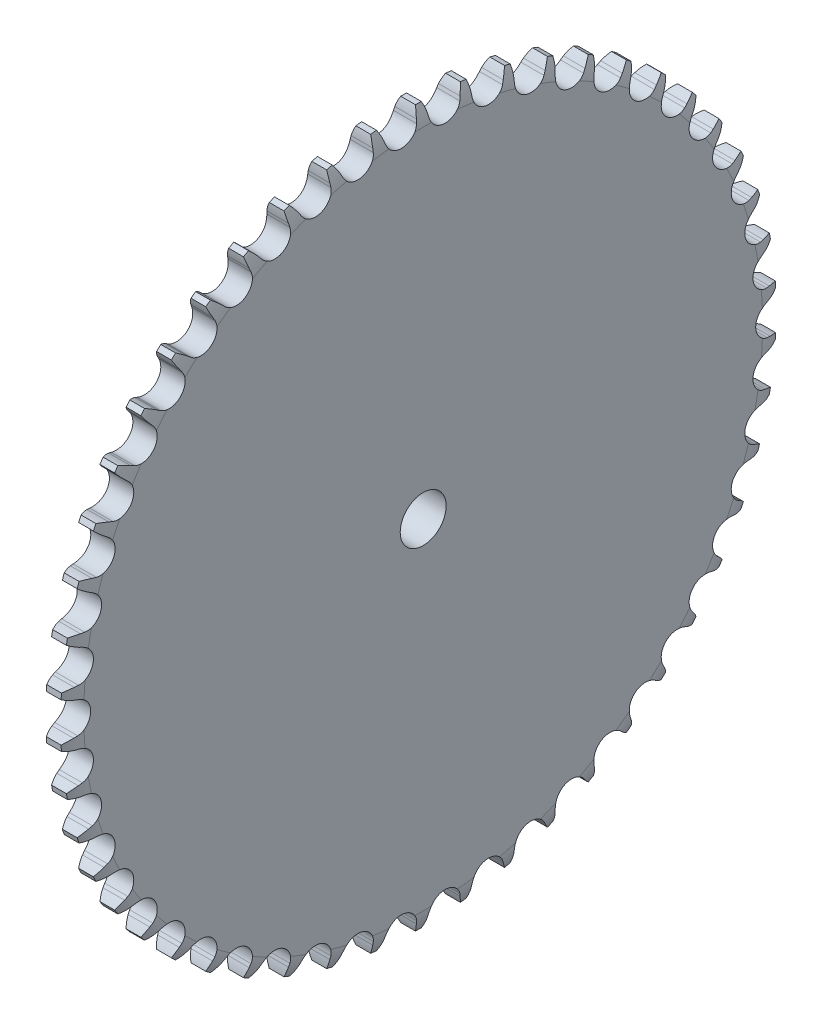
SolidWorks part; units mm, degrees
ref_plane "Front Plane" through (0, 0, 0) normal (0, 0, 1) x (1, 0, 0)
ref_plane "Top Plane" through (0, 0, 0) normal (0, 1, 0) x (1, 0, 0)
ref_plane "Right Plane" through (0, 0, 0) normal (1, 0, 0) x (0, 0, -1)
sketch "Sketch1" plane through (0, 0, 0) normal (0, 0, 1) x (1, 0, 0)
  line L0 (0, 0) -> (0, 73.8414)
  line L1 (-1.0423, 77.85) -> (-4.2577, 77.85)
  line L2 (-5.3, 73.8414) -> (-5.3, 20)
  line L3 (-5.3, 20) -> (-35.3, 20)
  line L4 (-35.3, 20) -> (-35.3, 0)
  line L5 (-35.3, 0) -> (0, 0)
  line L6 (0, 0) -> (22.8181, 0) construction
  arc A0 (-5.3, 73.8414) -> (-4.2577, 77.85) centre (4.6895, 73.3839) cw
  arc A1 (0, 73.8414) -> (-1.0423, 77.85) centre (-9.9895, 73.3839) ccw
  dimension "D5" = 10
  dimension "D1" = 35.3
  dimension "D2" = 30
  dimension "D3" = 20
  dimension "D4" = 155.7
revolve "Revolve1" add sketch "Sketch1" angle 360 about L6
sketch "Sketch2" plane through (-35.3, 0, 0) normal (-1, 0, 0) x (0, 0, 1)
  circle A0 centre (0, 0) radius 5
  dimension "D1" = 10
extrude "Cut-Extrude1" cut sketch "Sketch2" against normal blind 93
sketch "Sketch4" plane through (-35.3, 0, 0) normal (-1, 0, 0) x (0, 0, 1)
  line L0 (0, 0) -> (0, 75.845) construction
  line L1 (0, 0) -> (-4.7625, 75.6953) construction
  line L2 (0, 0) -> (4.7625, 75.6953) construction
  line L3 (-1.1837, 75.8358) -> (-1.3157, 75.0876)
  line L4 (1.1837, 75.8358) -> (1.3157, 75.0876)
  line L5 (-8.3306, 75.3861) -> (-8.106, 74.6603)
  arc A0 (-8.3306, 75.3861) -> (-1.1837, 75.8358) centre (0, 0) ccw
  arc A1 (-8.106, 74.6603) -> (-1.3157, 75.0876) centre (-4.7625, 75.6953) ccw
  circle A2 centre (4.7625, 75.6953) radius 3.5
  arc A3 (-1.1837, 75.8358) -> (-0.628, 77.8475) centre (9.6491, 73.9256) cw
  circle A4 centre (0, 0) radius 77.85 construction
  arc A5 (1.1837, 75.8358) -> (0.628, 77.8475) centre (-9.6491, 73.9256) ccw
  arc A6 (-8.3306, 75.3861) -> (-9.1342, 77.3123) centre (-18.8387, 72.1333) ccw
  arc A7 (-9.1342, 77.3123) -> (-0.628, 77.8475) centre (0, 0) cw
  dimension "D1" = 151.69
  dimension "D3" = 7
  dimension "D4" = 7
  dimension "D6" = 11
  dimension "D2" = 9.525
  dimension "D5" = 20
extrude "Cut-Extrude2" cut sketch "Sketch4" against normal blind 50 contours A7 A3 L3 A1 L5 A6
pattern_circular "CirPattern2" count 50 over 360 about axis through (0, 0, 0) along (1, 0, 0) of "Cut-Extrude2"
sketch "Sketch5" plane through (-35.3, 0, 0) normal (-1, 0, 0) x (0, 0, 1)
  circle A0 centre (0, 0) radius 20
extrude "Cut-Extrude3" cut sketch "Sketch5" against normal blind 30
sketch "Sketch6" plane through (-5.3, 0, 0) normal (-1, 0, 0) x (0, 0, 1)
  circle A0 centre (0, 0) radius 20
  dimension "D1" = 40
extrude "Boss-Extrude1" add sketch "Sketch6" along normal blind 10
sketch "Sketch8" plane through (-15.3, 0, 0) normal (-1, 0, 0) x (0, 0, 1)
  circle A0 centre (0, 0) radius 16.562
  circle A1 centre (0, 0) radius 15.922
  dimension "D1" = 33.124
  dimension "D2" = 31.844
sketch "Sketch11" plane through (-15.3, 0, 0) normal (-1, 0, 0) x (0, 0, 1)
  line L0 (0, 0) -> (0, 15.922) construction
  line L1 (0, 15.922) -> (0, 16.562) construction
  line L2 (0, 0) -> (0.9761, 15.8921) construction
  line L3 (0.9761, 15.8921) -> (1.0154, 16.5308) construction
  line L4 (-0.6409, 15.9091) -> (-0.4495, 16.5559)
  line L5 (0.6409, 15.9091) -> (0.4495, 16.5559)
  line L6 (1.3109, 15.8679) -> (1.58, 16.4865) construction
  line L7 (1.319, 15.8673) -> (1.5884, 16.4857)
  line L8 (2.5911, 15.7098) -> (2.4806, 16.3752)
  line L9 (3.2589, 15.5849) -> (3.6023, 16.1655)
  line L10 (4.502, 15.2723) -> (4.4741, 15.9462)
  line L11 (5.1494, 15.0663) -> (5.5615, 15.6003)
  line L12 (6.3447, 14.6033) -> (6.3998, 15.2755)
  line L13 (6.9618, 14.3193) -> (7.4365, 14.7986)
  line L14 (8.0911, 13.7129) -> (8.2285, 14.3733)
  line L15 (8.6688, 13.3553) -> (9.1987, 13.7726)
  line L16 (9.715, 12.6147) -> (9.9324, 13.2532)
  line L17 (10.2443, 12.1887) -> (10.8215, 12.5378)
  line L18 (11.1915, 11.3252) -> (11.4858, 11.9321)
  line L19 (11.6645, 10.8375) -> (12.2802, 11.1129)
  line L20 (12.4984, 9.864) -> (12.8651, 10.4302)
  line L21 (12.9078, 9.3219) -> (13.5527, 9.5196)
  line L22 (13.6159, 8.2534) -> (14.0493, 8.7702)
  line L23 (13.9556, 7.665) -> (14.6199, 7.782)
  line L24 (14.5269, 6.5176) -> (15.0206, 6.9772)
  line L25 (14.7917, 5.8919) -> (15.4654, 5.9264)
  line L26 (15.2177, 4.683) -> (15.7642, 5.0785)
  line L27 (15.4037, 4.0296) -> (16.0764, 3.9809)
  line L28 (15.6779, 2.7774) -> (16.2688, 3.1028)
  line L29 (15.7821, 2.1061) -> (16.4438, 1.9752)
  line L30 (15.9004, 0.8297) -> (16.5267, 1.08)
  line L31 (15.9213, 0.1507) -> (16.5619, -0.0606)
  line L32 (15.8818, -1.1305) -> (16.5342, -0.9591)
  line L33 (15.8191, -1.807) -> (16.4289, -2.0954)
  line L34 (15.6225, -3.0736) -> (16.291, -2.9837)
  line L35 (15.4772, -3.7373) -> (16.0469, -4.0984)
  line L36 (15.1264, -4.9702) -> (15.8009, -4.9631)
  line L37 (14.9006, -5.6109) -> (15.4216, -6.0393)
  line L38 (14.401, -6.7914) -> (15.0712, -6.8672)
  line L39 (14.0981, -7.3995) -> (14.5626, -7.8887)
  line L40 (13.4572, -8.5096) -> (14.1131, -8.6672)
  line L41 (13.082, -9.0759) -> (13.4828, -9.6184)
  line L42 (12.3095, -10.0988) -> (12.941, -10.3359)
  line L43 (11.8675, -10.6147) -> (12.1986, -11.2024)
  line L44 (10.9752, -11.535) -> (11.5728, -11.8478)
  line L45 (10.4731, -11.9927) -> (10.7295, -12.6166)
  line L46 (9.4745, -12.7963) -> (10.0291, -13.1802)
  line L47 (8.92, -13.1888) -> (9.0977, -13.8395)
  line L48 (7.8301, -13.8636) -> (8.3334, -14.3127)
  line L49 (7.2316, -14.185) -> (7.3281, -14.8526)
  line L50 (6.0671, -14.7207) -> (6.5114, -15.2283)
  line L51 (5.4336, -14.9662) -> (5.4473, -15.6405)
  line L52 (4.2121, -15.3547) -> (4.5906, -15.9131)
  line L53 (3.5533, -15.5204) -> (3.484, -16.1914)
  line L54 (2.2933, -15.756) -> (2.6003, -16.3566)
  line L55 (1.6191, -15.8395) -> (1.4678, -16.4968)
  line L56 (0.3397, -15.9184) -> (0.5705, -16.5522)
  line L57 (-0.3397, -15.9184) -> (-0.5705, -16.5522)
  line L58 (-1.6191, -15.8395) -> (-1.4678, -16.4968)
  line L59 (-2.2933, -15.756) -> (-2.6003, -16.3566)
  line L60 (-3.5533, -15.5204) -> (-3.484, -16.1914)
  line L61 (-4.2121, -15.3547) -> (-4.5906, -15.9131)
  line L62 (-5.4336, -14.9662) -> (-5.4473, -15.6405)
  line L63 (-6.0671, -14.7207) -> (-6.5114, -15.2283)
  line L64 (-7.2316, -14.185) -> (-7.3281, -14.8526)
  line L65 (-7.8301, -13.8636) -> (-8.3334, -14.3127)
  line L66 (-8.92, -13.1888) -> (-9.0977, -13.8395)
  line L67 (-9.4745, -12.7963) -> (-10.0291, -13.1802)
  line L68 (-10.4731, -11.9927) -> (-10.7295, -12.6166)
  line L69 (-10.9752, -11.535) -> (-11.5728, -11.8478)
  line L70 (-11.8675, -10.6147) -> (-12.1986, -11.2024)
  line L71 (-12.3095, -10.0988) -> (-12.941, -10.3359)
  line L72 (-13.082, -9.0759) -> (-13.4828, -9.6184)
  line L73 (-13.4572, -8.5096) -> (-14.1131, -8.6672)
  line L74 (-14.0981, -7.3995) -> (-14.5626, -7.8887)
  line L75 (-14.401, -6.7914) -> (-15.0712, -6.8672)
  line L76 (-14.9006, -5.6109) -> (-15.4216, -6.0393)
  line L77 (-15.1264, -4.9702) -> (-15.8009, -4.9631)
  line L78 (-15.4772, -3.7373) -> (-16.0469, -4.0984)
  line L79 (-15.6225, -3.0736) -> (-16.291, -2.9837)
  line L80 (-15.8191, -1.807) -> (-16.4289, -2.0954)
  line L81 (-15.8818, -1.1305) -> (-16.5342, -0.9591)
  line L82 (-15.9213, 0.1507) -> (-16.5619, -0.0606)
  line L83 (-15.9004, 0.8297) -> (-16.5267, 1.08)
  line L84 (-15.7821, 2.1061) -> (-16.4438, 1.9752)
  line L85 (-15.6779, 2.7774) -> (-16.2688, 3.1028)
  line L86 (-15.4037, 4.0296) -> (-16.0764, 3.9809)
  line L87 (-15.2177, 4.683) -> (-15.7642, 5.0785)
  line L88 (-14.7917, 5.8919) -> (-15.4654, 5.9264)
  line L89 (-14.5269, 6.5176) -> (-15.0206, 6.9772)
  line L90 (-13.9556, 7.665) -> (-14.6199, 7.782)
  line L91 (-13.6159, 8.2534) -> (-14.0493, 8.7702)
  line L92 (-12.9078, 9.3219) -> (-13.5527, 9.5196)
  line L93 (-12.4984, 9.864) -> (-12.8651, 10.4302)
  line L94 (-11.6645, 10.8375) -> (-12.2802, 11.1129)
  line L95 (-11.1915, 11.3252) -> (-11.4858, 11.9321)
  line L96 (-10.2443, 12.1887) -> (-10.8215, 12.5378)
  line L97 (-9.715, 12.6147) -> (-9.9324, 13.2532)
  line L98 (-8.6688, 13.3553) -> (-9.1987, 13.7726)
  line L99 (-8.0911, 13.7129) -> (-8.2285, 14.3733)
  line L100 (-6.9618, 14.3193) -> (-7.4365, 14.7986)
  line L101 (-6.3447, 14.6033) -> (-6.3998, 15.2755)
  line L102 (-5.1494, 15.0663) -> (-5.5615, 15.6003)
  line L103 (-4.502, 15.2723) -> (-4.4741, 15.9462)
  line L104 (-3.2589, 15.5849) -> (-3.6023, 16.1655)
  line L105 (-2.5911, 15.7098) -> (-2.4806, 16.3752)
  line L106 (-1.319, 15.8673) -> (-1.5884, 16.4857)
  circle A0 centre (0, 0) radius 15.922 construction
  circle A1 centre (0, 0) radius 16.562 construction
  arc A2 (0.4495, 16.5559) -> (0, 16.562) centre (0, 0) ccw
  arc A4 (-0.6409, 15.9091) -> (-1.319, 15.8673) centre (0, 0) ccw
  arc A5 (0.4495, 16.5559) -> (-0.4495, 16.5559) centre (0, 0) ccw
  arc A6 (2.4806, 16.3752) -> (1.5884, 16.4857) centre (0, 0) ccw
  arc A7 (4.4741, 15.9462) -> (3.6023, 16.1655) centre (0, 0) ccw
  arc A8 (6.3998, 15.2755) -> (5.5615, 15.6003) centre (0, 0) ccw
  arc A9 (8.2285, 14.3733) -> (7.4365, 14.7986) centre (0, 0) ccw
  arc A10 (9.9324, 13.2532) -> (9.1987, 13.7726) centre (0, 0) ccw
  arc A11 (11.4858, 11.9321) -> (10.8215, 12.5378) centre (0, 0) ccw
  arc A12 (12.8651, 10.4302) -> (12.2802, 11.1129) centre (0, 0) ccw
  arc A13 (14.0493, 8.7702) -> (13.5527, 9.5196) centre (0, 0) ccw
  arc A14 (15.0206, 6.9772) -> (14.6199, 7.782) centre (0, 0) ccw
  arc A15 (15.7642, 5.0785) -> (15.4654, 5.9264) centre (0, 0) ccw
  arc A16 (16.2688, 3.1028) -> (16.0764, 3.9809) centre (0, 0) ccw
  arc A17 (16.5267, 1.08) -> (16.4438, 1.9752) centre (0, 0) ccw
  arc A18 (16.5342, -0.9591) -> (16.5619, -0.0606) centre (0, 0) ccw
  arc A19 (16.291, -2.9837) -> (16.4289, -2.0954) centre (0, 0) ccw
  arc A20 (15.8009, -4.9631) -> (16.0469, -4.0984) centre (0, 0) ccw
  arc A21 (15.0712, -6.8672) -> (15.4216, -6.0393) centre (0, 0) ccw
  arc A22 (14.1131, -8.6672) -> (14.5626, -7.8887) centre (0, 0) ccw
  arc A23 (12.941, -10.3359) -> (13.4828, -9.6184) centre (0, 0) ccw
  arc A24 (11.5728, -11.8478) -> (12.1986, -11.2024) centre (0, 0) ccw
  arc A25 (10.0291, -13.1802) -> (10.7295, -12.6166) centre (0, 0) ccw
  arc A26 (8.3334, -14.3127) -> (9.0977, -13.8395) centre (0, 0) ccw
  arc A27 (6.5114, -15.2283) -> (7.3281, -14.8526) centre (0, 0) ccw
  arc A28 (4.5906, -15.9131) -> (5.4473, -15.6405) centre (0, 0) ccw
  arc A29 (2.6003, -16.3566) -> (3.484, -16.1914) centre (0, 0) ccw
  arc A30 (0.5705, -16.5522) -> (1.4678, -16.4968) centre (0, 0) ccw
  arc A31 (-1.4678, -16.4968) -> (-0.5705, -16.5522) centre (0, 0) ccw
  arc A32 (-3.484, -16.1914) -> (-2.6003, -16.3566) centre (0, 0) ccw
  arc A33 (-5.4473, -15.6405) -> (-4.5906, -15.9131) centre (0, 0) ccw
  arc A34 (-7.3281, -14.8526) -> (-6.5114, -15.2283) centre (0, 0) ccw
  arc A35 (-9.0977, -13.8395) -> (-8.3334, -14.3127) centre (0, 0) ccw
  arc A36 (-10.7295, -12.6166) -> (-10.0291, -13.1802) centre (0, 0) ccw
  arc A37 (-12.1986, -11.2024) -> (-11.5728, -11.8478) centre (0, 0) ccw
  arc A38 (-13.4828, -9.6184) -> (-12.941, -10.3359) centre (0, 0) ccw
  arc A39 (-14.5626, -7.8887) -> (-14.1131, -8.6672) centre (0, 0) ccw
  arc A40 (-15.4216, -6.0393) -> (-15.0712, -6.8672) centre (0, 0) ccw
  arc A41 (-16.0469, -4.0984) -> (-15.8009, -4.9631) centre (0, 0) ccw
  arc A42 (-16.4289, -2.0954) -> (-16.291, -2.9837) centre (0, 0) ccw
  arc A43 (-16.5619, -0.0606) -> (-16.5342, -0.9591) centre (0, 0) ccw
  arc A44 (-16.4438, 1.9752) -> (-16.5267, 1.08) centre (0, 0) ccw
  arc A45 (-16.0764, 3.9809) -> (-16.2688, 3.1028) centre (0, 0) ccw
  arc A46 (-15.4654, 5.9264) -> (-15.7642, 5.0785) centre (0, 0) ccw
  arc A47 (-14.6199, 7.782) -> (-15.0206, 6.9772) centre (0, 0) ccw
  arc A48 (-13.5527, 9.5196) -> (-14.0493, 8.7702) centre (0, 0) ccw
  arc A49 (-12.2802, 11.1129) -> (-12.8651, 10.4302) centre (0, 0) ccw
  arc A50 (-10.8215, 12.5378) -> (-11.4858, 11.9321) centre (0, 0) ccw
  arc A51 (-9.1987, 13.7726) -> (-9.9324, 13.2532) centre (0, 0) ccw
  arc A52 (-7.4365, 14.7986) -> (-8.2285, 14.3733) centre (0, 0) ccw
  arc A53 (-5.5615, 15.6003) -> (-6.3998, 15.2755) centre (0, 0) ccw
  arc A54 (-3.6023, 16.1655) -> (-4.4741, 15.9462) centre (0, 0) ccw
  arc A55 (-1.5884, 16.4857) -> (-2.4806, 16.3752) centre (0, 0) ccw
  arc A56 (-4.502, 15.2723) -> (-5.1494, 15.0663) centre (0, 0) ccw
  arc A57 (-2.5911, 15.7098) -> (-3.2589, 15.5849) centre (0, 0) ccw
  arc A58 (-6.3447, 14.6033) -> (-6.9618, 14.3193) centre (0, 0) ccw
  arc A59 (1.319, 15.8673) -> (0.6409, 15.9091) centre (0, 0) ccw
  arc A60 (3.2589, 15.5849) -> (2.5911, 15.7098) centre (0, 0) ccw
  arc A61 (5.1494, 15.0663) -> (4.502, 15.2723) centre (0, 0) ccw
  arc A62 (6.9618, 14.3193) -> (6.3447, 14.6033) centre (0, 0) ccw
  arc A63 (8.6688, 13.3553) -> (8.0911, 13.7129) centre (0, 0) ccw
  arc A64 (10.2443, 12.1887) -> (9.715, 12.6147) centre (0, 0) ccw
  arc A65 (11.6645, 10.8375) -> (11.1915, 11.3252) centre (0, 0) ccw
  arc A66 (12.9078, 9.3219) -> (12.4984, 9.864) centre (0, 0) ccw
  arc A67 (13.9556, 7.665) -> (13.6159, 8.2534) centre (0, 0) ccw
  arc A68 (14.7917, 5.8919) -> (14.5269, 6.5176) centre (0, 0) ccw
  arc A69 (15.4037, 4.0296) -> (15.2177, 4.683) centre (0, 0) ccw
  arc A70 (15.7821, 2.1061) -> (15.6779, 2.7774) centre (0, 0) ccw
  arc A71 (15.8191, -1.807) -> (15.8818, -1.1305) centre (0, 0) ccw
  arc A72 (15.9213, 0.1507) -> (15.9004, 0.8297) centre (0, 0) ccw
  arc A73 (15.4772, -3.7373) -> (15.6225, -3.0736) centre (0, 0) ccw
  arc A74 (14.9006, -5.6109) -> (15.1264, -4.9702) centre (0, 0) ccw
  arc A75 (14.0981, -7.3995) -> (14.401, -6.7914) centre (0, 0) ccw
  arc A76 (13.082, -9.0759) -> (13.4572, -8.5096) centre (0, 0) ccw
  arc A77 (11.8675, -10.6147) -> (12.3095, -10.0988) centre (0, 0) ccw
  arc A78 (7.2316, -14.185) -> (7.8301, -13.8636) centre (0, 0) ccw
  arc A79 (8.92, -13.1888) -> (9.4745, -12.7963) centre (0, 0) ccw
  arc A80 (10.4731, -11.9927) -> (10.9752, -11.535) centre (0, 0) ccw
  arc A81 (5.4336, -14.9662) -> (6.0671, -14.7207) centre (0, 0) ccw
  arc A82 (3.5533, -15.5204) -> (4.2121, -15.3547) centre (0, 0) ccw
  arc A83 (1.6191, -15.8395) -> (2.2933, -15.756) centre (0, 0) ccw
  arc A84 (-0.3397, -15.9184) -> (0.3397, -15.9184) centre (0, 0) ccw
  arc A85 (-2.2933, -15.756) -> (-1.6191, -15.8395) centre (0, 0) ccw
  arc A86 (-4.2121, -15.3547) -> (-3.5533, -15.5204) centre (0, 0) ccw
  arc A87 (-6.0671, -14.7207) -> (-5.4336, -14.9662) centre (0, 0) ccw
  arc A88 (-7.8301, -13.8636) -> (-7.2316, -14.185) centre (0, 0) ccw
  arc A89 (-9.4745, -12.7963) -> (-8.92, -13.1888) centre (0, 0) ccw
  arc A90 (-10.9752, -11.535) -> (-10.4731, -11.9927) centre (0, 0) ccw
  arc A91 (-12.3095, -10.0988) -> (-11.8675, -10.6147) centre (0, 0) ccw
  arc A92 (-13.4572, -8.5096) -> (-13.082, -9.0759) centre (0, 0) ccw
  arc A93 (-14.401, -6.7914) -> (-14.0981, -7.3995) centre (0, 0) ccw
  arc A94 (-15.1264, -4.9702) -> (-14.9006, -5.6109) centre (0, 0) ccw
  arc A95 (-15.6225, -3.0736) -> (-15.4772, -3.7373) centre (0, 0) ccw
  arc A96 (-15.8818, -1.1305) -> (-15.8191, -1.807) centre (0, 0) ccw
  arc A97 (-15.9004, 0.8297) -> (-15.9213, 0.1507) centre (0, 0) ccw
  arc A98 (-15.6779, 2.7774) -> (-15.7821, 2.1061) centre (0, 0) ccw
  arc A99 (-15.2177, 4.683) -> (-15.4037, 4.0296) centre (0, 0) ccw
  arc A100 (-14.5269, 6.5176) -> (-14.7917, 5.8919) centre (0, 0) ccw
  arc A101 (-13.6159, 8.2534) -> (-13.9556, 7.665) centre (0, 0) ccw
  arc A102 (-12.4984, 9.864) -> (-12.9078, 9.3219) centre (0, 0) ccw
  arc A103 (-11.1915, 11.3252) -> (-11.6645, 10.8375) centre (0, 0) ccw
  arc A104 (-9.715, 12.6147) -> (-10.2443, 12.1887) centre (0, 0) ccw
  arc A105 (-8.0911, 13.7129) -> (-8.6688, 13.3553) centre (0, 0) ccw
  dimension "D1" = 1.016
  dimension "D2" = 20
  dimension "D3" = 0.67
  dimension "D4" = 51
extrude "Boss-Extrude3" add sketch "Sketch11" along normal blind 6.5 contours L5 A59 L7 A6 L8 A60 L9 A7 L10 A61 L11 A8 L12 A62 L13 A9 L14 A63 L15 A10 L16 A64 L17 A11 L18 A65 L19 A12 L20 A66 L21 A13 L22 A67 L23 A14 L24 A68 L25 A15 L26 A69 L27 A16 L28 A70 L29 A17 L30 A72 L31 A18 L32 A71 L33 A19 L34 A73 L35 A20 L36 A74 L37 A21 L38 A75 L39 A22 L40 A76 L41 A23 L42 A77 L43 A24 L44 A80 L45 A25 L46 A79 L47 A26 L48 A78 L49 A27 L50 A81 L51 A28 L52 A82 L53 A29 L54 A83 L55 A30 L56 A84 L57 A31 L58 A85 L59 A32 L60 A86 L61 A33 L62 A87 L63 A34 L64 A88 L65 A35 L66 A89 L67 A36 L68 A90 L69 A37 L70 A91 L71 A38 L72 A92 L73 A39 L74 A93 L75 A40 L76 A94 L77 A41 L78 A95 L79 A42 L80 A96 L81 A43 L82 A97 L83 A44 L84 A98 L85 A45 L86 A99 L87 A46 L88 A100 L89 A47 L90 A101 L91 A48 L92 A102 L93 A49 L94 A103 L95 A50 L96 A104 L97 A51 L98 A105 L99 A52 L100 A58 L101 A53 L102 A56 L103 A54 L104 A57 L105 A55 L106 A4 L4 A5
fillet "Fillet1" radius 0.23 99 edges at (-18.55, 14.6033, -6.3447) (-18.55, 14.3193, -6.9618) (-18.55, 14.3733, -8.2285) (-18.55, 13.3553, -8.6688) (-18.55, 12.1887, -10.2443) (-18.55, 10.8375, -11.6645) (-18.55, 9.3219, -12.9078) (-18.55, 9.5196, -13.5527) (-18.55, 8.7702, -14.0493) (-18.55, 7.665, -13.9556) (-18.55, 6.5176, -14.5269) (-18.55, 5.0785, -15.7642) (-18.55, 4.0296, -15.4037) (-18.55, 2.1061, -15.7821) (-18.55, 1.08, -16.5267) (-18.55, 0.8297, -15.9004) (-18.55, -0.9591, -16.5342) (-18.55, -1.1305, -15.8818) (-18.55, -2.0954, -16.4289) (-18.55, -1.807, -15.8191) (-18.55, -3.7373, -15.4772) (-18.55, -4.0984, -16.0469) (-18.55, -4.9702, -15.1264) (-18.55, -5.6109, -14.9006) (-18.55, -6.8672, -15.0712) (-18.55, -7.3995, -14.0981) (-18.55, -8.6672, -14.1131) (-18.55, -8.5096, -13.4572) (-18.55, -10.3359, -12.941) (-18.55, -10.6147, -11.8675) (-18.55, -11.2024, -12.1986) (-18.55, -11.535, -10.9752) (-18.55, -12.6166, -10.7295) (-18.55, -13.1802, -10.0291) (-18.55, -13.1888, -8.92) (-18.55, -14.3127, -8.3334) (-18.55, -13.8636, -7.8301) (-18.55, -14.7207, -6.0671) (-18.55, -14.9662, -5.4336) (-18.55, -15.6405, -5.4473) (-18.55, -15.5204, -3.5533) (-18.55, -16.1914, -3.484) (-18.55, -16.3566, -2.6003) (-18.55, -15.8395, -1.6191) (-18.55, -16.4968, -1.4678) (-18.55, -15.9184, -0.3397) (-18.55, -16.5522, 0.5705) (-18.55, -16.3566, 2.6003) (-18.55, -15.6405, 5.4473) (-18.55, -14.7207, 6.0671) (-18.55, -14.185, 7.2316) (-18.55, -13.8636, 7.8301) (-18.55, -14.3127, 8.3334) (-18.55, -13.1888, 8.92) (-18.55, -13.1802, 10.0291) (-18.55, -12.6166, 10.7295) (-18.55, -11.9927, 10.4731) (-18.55, -10.6147, 11.8675) (-18.55, -8.5096, 13.4572) (-18.55, -9.0759, 13.082) (-18.55, -9.6184, 13.4828) (-18.55, -6.8672, 15.0712) (-18.55, -6.0393, 15.4216) (-18.55, -4.9631, 15.8009) (-18.55, -4.0984, 16.0469) (-18.55, -2.9837, 16.291) (-18.55, -3.0736, 15.6225) (-18.55, -2.0954, 16.4289) (-18.55, -1.807, 15.8191) (-18.55, -0.9591, 16.5342) (-18.55, -1.1305, 15.8818) (-18.55, -0.0606, 16.5619) (-18.55, 0.8297, 15.9004) (-18.55, 3.1028, 16.2688) (-18.55, 2.7774, 15.6779) (-18.55, 4.0296, 15.4037) (-18.55, 4.683, 15.2177) (-18.55, 5.8919, 14.7917) (-18.55, 8.2534, 13.6159) (-18.55, 10.4302, 12.8651) (-18.55, 9.864, 12.4984) (-18.55, 11.1129, 12.2802) (-18.55, 10.8375, 11.6645) (-18.55, 11.3252, 11.1915) (-18.55, 12.5378, 10.8215) (-18.55, 12.6147, 9.715) (-18.55, 13.2532, 9.9324) (-18.55, 13.7726, 9.1987) (-18.55, 13.7129, 8.0911) (-18.55, 14.7986, 7.4365) (-18.55, 14.6033, 6.3447) (-18.55, 15.2723, 4.502) (-18.55, 15.7098, 2.5911) (-18.55, 15.8673, -1.319) (-18.55, 15.9091, -0.6409) (-18.55, 15.5849, -3.2589) (-18.55, 16.5559, -0.4495) (-18.55, 16.3752, -2.4806) (-18.55, 15.9462, -4.4741)
sketch "Sketch12" plane through (-21.8, 0, 0) normal (-1, 0, 0) x (0, 0, 1)
  circle A0 centre (0, 0) radius 20
extrude "Boss-Extrude4" add sketch "Sketch12" along normal blind 20
sketch "Sketch13" plane through (-41.8, 0, 0) normal (-1, 0, 0) x (0, 0, 1)
  circle A0 centre (0, 0) radius 5
  dimension "D1" = 10
extrude "Cut-Extrude4" cut sketch "Sketch13" against normal blind 40
sketch "Sketch14" plane through (-41.8, 0, 0) normal (-1, 0, 0) x (0, 0, 1)
  line L3 (0, 7) -> (-2.85, 7)
  line L4 (-2.85, 7) -> (-2.85, 9.5)
  line L5 (-2.85, 9.5) -> (2.85, 9.5)
  line L6 (2.85, 9.5) -> (2.85, 7)
  line L7 (2.85, 7) -> (0, 7)
  line L8 (6.0622, -3.5) -> (7.4872, -1.0318)
  line L9 (7.4872, -1.0318) -> (9.6522, -2.2818)
  line L10 (9.6522, -2.2818) -> (6.8022, -7.2182)
  line L13 (-6.0622, -3.5) -> (-4.6372, -5.9682)
  line L14 (-4.6372, -5.9682) -> (-6.8022, -7.2182)
  line L15 (-6.8022, -7.2182) -> (-9.6522, -2.2818)
  line L18 (6.8022, -7.2182) -> (4.6372, -5.9682)
  line L19 (4.6372, -5.9682) -> (6.0622, -3.5)
  line L20 (-9.6522, -2.2818) -> (-7.4872, -1.0318)
  line L21 (-7.4872, -1.0318) -> (-6.0622, -3.5)
  dimension "D6" = 5.7
  dimension "D7" = 2.85
  dimension "D8" = 2.5
  dimension "D9" = 2.5
  dimension "D10" = 5.7
  dimension "D11" = 2.5
  dimension "D12" = 5.7
  dimension "D13" = 2.85
  dimension "D14" = 2.85
extrude "Cut-Extrude5" cut sketch "Sketch14" against normal blind 12.85 contours L8 L9 L10 L18 L19 | L13 L14 L15 L20 L21 | L3 L4 L5 L6 L7
ref_plane "Plane1" through (0, -10, 17.3205) normal (0, -0.5, 0.866) x (1, 0, 0)
sketch "Sketch15" plane through (0, -10, 17.3205) normal (0, -0.5, 0.866) x (1, 0, 0)
  circle A0 centre (-31.8, 0) radius 3
  dimension "D1" = 6
extrude "Cut-Extrude6" cut sketch "Sketch15" against normal blind 4.5
sketch "Sketch16" plane through (0, -7.75, 13.4234) normal (0, -0.5, 0.866) x (1, 0, 0)
  circle A0 centre (-31.8, 0) radius 1.8
  dimension "D1" = 3.6
extrude "Cut-Extrude7" cut sketch "Sketch16" against normal up to next
sketch "Sketch17" plane through (0, -3.5, 6.0622) normal (0, -0.5, 0.866) x (1, 0, 0)
  circle A0 centre (-31.8, 0) radius 1.8
  dimension "D1" = 3.6
extrude "Cut-Extrude8" cut sketch "Sketch17" against normal up to next
ref_plane "Plane3" through (0, 20, 0) normal (0, 1, 0) x (1, 0, 0)
sketch "Sketch22" plane through (0, 20, 0) normal (0, 1, 0) x (1, 0, 0)
  circle A0 centre (-31.8, 0) radius 3
  dimension "D1" = 6
extrude "Cut-Extrude12" cut sketch "Sketch22" against normal blind 4.5
sketch "Sketch23" plane through (0, 15.5, 0) normal (0, 1, 0) x (1, 0, 0)
  circle A0 centre (-31.8, 0) radius 1.8
  dimension "D1" = 3.6
extrude "Cut-Extrude13" cut sketch "Sketch23" against normal up to next
sketch "Sketch24" plane through (0, 7, 0) normal (0, 1, 0) x (1, 0, 0)
  circle A0 centre (-31.8, 0) radius 1.8
  dimension "D1" = 3.6
extrude "Cut-Extrude14" cut sketch "Sketch24" against normal up to next
ref_plane "Plane4" through (0, -10, -17.3205) normal (0, -0.5, -0.866) x (1, 0, 0)
sketch "Sketch25" plane through (0, -10, -17.3205) normal (0, -0.5, -0.866) x (1, 0, 0)
  circle A0 centre (-31.8, 0) radius 3
  dimension "D1" = 6
extrude "Cut-Extrude15" cut sketch "Sketch25" against normal blind 4.5
sketch "Sketch26" plane through (0, -7.75, -13.4234) normal (0, -0.5, -0.866) x (-1, 0, 0)
  circle A0 centre (31.8, 0) radius 1.8
  dimension "D1" = 3.6
extrude "Cut-Extrude16" cut sketch "Sketch26" against normal up to next
sketch "Sketch27" plane through (0, -3.5, -6.0622) normal (0, -0.5, -0.866) x (-1, 0, 0)
  circle A0 centre (31.8, 0) radius 1.8
  dimension "D1" = 3.6
extrude "Cut-Extrude17" cut sketch "Sketch27" against normal up to next
